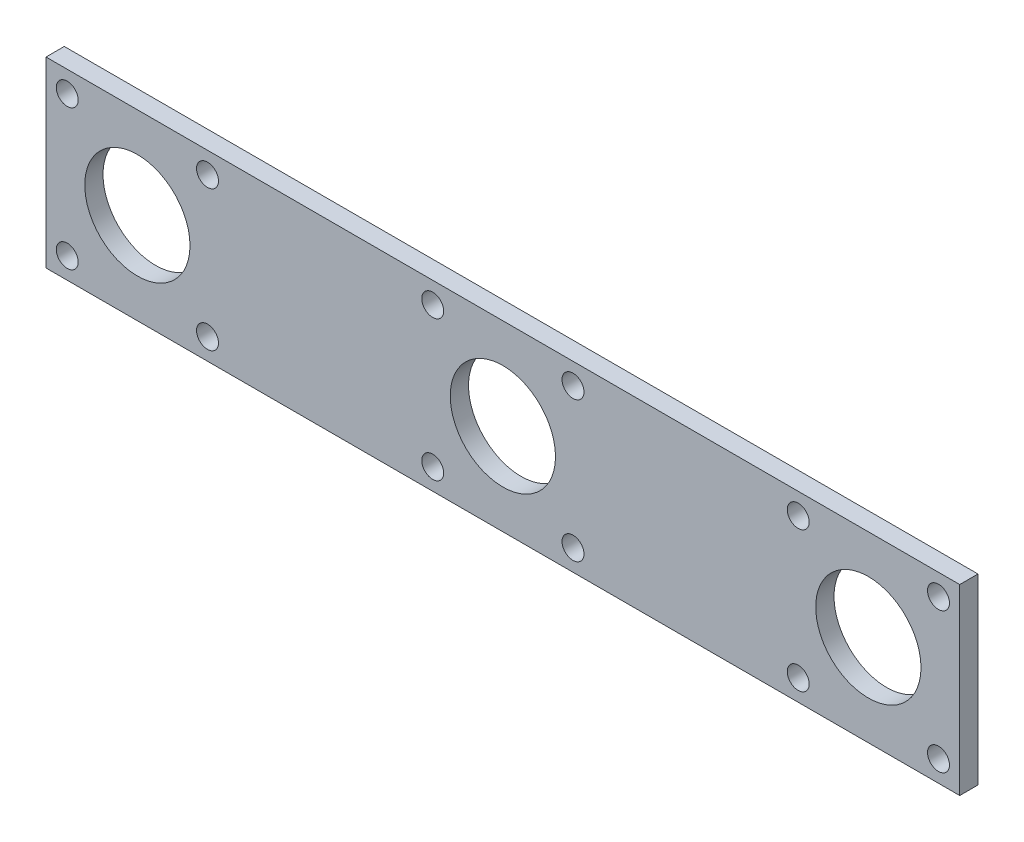
SolidWorks part; units mm, degrees
ref_plane "Front Plane" through (0, 0, 0) normal (0, 0, 1) x (1, 0, 0)
ref_plane "Top Plane" through (0, 0, 0) normal (0, 1, 0) x (1, 0, 0)
ref_plane "Right Plane" through (0, 0, 0) normal (1, 0, 0) x (0, 0, -1)
sketch "Sketch1" plane through (0, 0, 0) normal (0, 0, 1) x (1, 0, 0)
  line L19 (-63.5, -12.7) -> (63.5, -12.7)
  line L20 (-63.5, -12.7) -> (-63.5, 12.7)
  line L21 (-63.5, 12.7) -> (63.5, 12.7)
  line L22 (63.5, -12.7) -> (63.5, 12.7)
  line L23 (-63.5, -12.7) -> (63.5, 12.7) construction
  line L24 (-63.5, 12.7) -> (63.5, -12.7) construction
  circle A0 centre (0, 0) radius 7.3152
  circle A1 centre (9.7484, 9.7484) radius 1.524
  circle A2 centre (-9.7484, -9.7484) radius 1.524
  circle A3 centre (9.7484, -9.7484) radius 1.524
  circle A4 centre (-9.7484, 9.7484) radius 1.524
  circle A10 centre (50.8, 0) radius 7.3152
  circle A11 centre (60.5484, 9.7484) radius 1.524
  circle A12 centre (41.0516, -9.7484) radius 1.524
  circle A13 centre (60.5484, -9.7484) radius 1.524
  circle A14 centre (41.0516, 9.7484) radius 1.524
  circle A15 centre (-50.8, 0) radius 7.3152
  circle A16 centre (-41.0516, 9.7484) radius 1.524
  circle A17 centre (-60.5484, -9.7484) radius 1.524
  circle A18 centre (-41.0516, -9.7484) radius 1.524
  circle A19 centre (-60.5484, 9.7484) radius 1.524
extrude "Boss-Extrude7" add sketch "Sketch1" along normal blind 2.54
